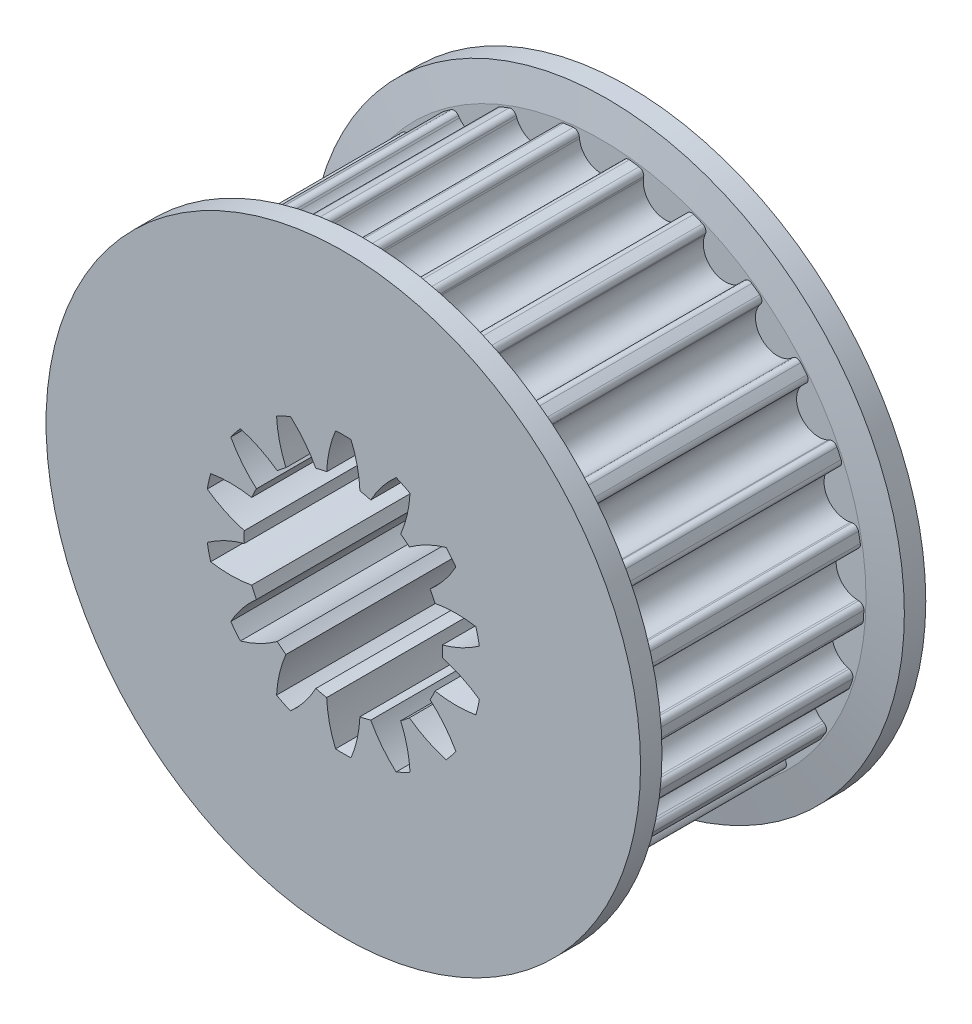
SolidWorks part; units mm, degrees
material "PETG"
ref_plane "Front Plane" through (0, 0, 0) normal (0, 0, 1) x (1, 0, 0)
ref_plane "Top Plane" through (0, 0, 0) normal (0, 1, 0) x (1, 0, 0)
ref_plane "Right Plane" through (0, 0, 0) normal (1, 0, 0) x (0, 0, -1)
sketch "Sketch2" plane through (0, 0, 0) normal (0, 0, 1) x (1, 0, 0)
  circle A0 centre (0, 0) radius 19.3468
  dimension "D1" = 38.6936
extrude "pulley" add sketch "Sketch2" along normal mid plane 17
sketch "tooth" plane through (0, 0, 0) normal (0, 0, 1) x (1, 0, 0)
  line L0 (0, 0) -> (0, 18.9468) construction
  line L1 (4.9563, 18.2871) -> (0, 18.9468) construction
  line L2 (4.9563, 18.2871) -> (0, 0) construction
  line L3 (-2.1327, 22.9824) -> (-1.6129, 18.7488)
  line L6 (2.1327, 22.9824) -> (1.6129, 18.7488)
  line L7 (-2.1327, 22.9824) -> (2.1327, 22.9824)
  arc A1 (-1.6129, 18.7488) -> (1.6129, 18.7488) centre (0, 18.9468) ccw
  arc A2 (0, 18.9468) -> (4.9563, 18.2871) centre (0, 0) cw construction
  circle A3 centre (4.9563, 18.2871) radius 1.625 construction
  dimension "D1" = 18.9468
  dimension "D2" = 3.25
  dimension "D3" = 5
  dimension "D5" = 14
extrude "cut tooth" cut sketch "tooth" against normal mid plane 17
fillet "blend tooth" radius 0.4 2 edges at (1.6774, 19.274, 0) (-1.6774, 19.274, 0)
pattern_circular "tooth pattern" count 25 over 360 about axis through (0, 0, 0) along (0, 0, 1) of "cut tooth", "blend tooth"
sketch "Sketch3" plane through (0, 0, 0) normal (0, 0, 1) x (1, 0, 0)
  circle A0 centre (0, 0) radius 21.8868
  circle A1 centre (0, 0) radius 19.3468 construction
  dimension "D1" = 2.54
extrude "sidewall" add sketch "Sketch3" along normal blind 2 from offset 8.5
mirror "mirror sidewall" about plane through (0, 0, 0) normal (0, 0, 1) of "sidewall"
chamfer "sidewall chamfer" distance 2.4 angle 10 2 edges at (21.8868, 0, 8.5) (21.8868, 0, -8.5)
sketch "Sketch5" plane through (0, 0, 0) normal (0, 0, 1) x (1, 0, 0)
  circle A0 centre (0, 0) radius 9.525
  dimension "D1" = 19.05
extrude "bearing spacer (Manual Suppress)" add sketch "Sketch5" along normal blind 10.55 and the other way blind 10.55
sketch "Sketch6" plane through (0, 0, -10.5) normal (0, 0, -1) x (-1, 0, 0)
  arc A57 (2.0216, -7.0171) -> (3.8881, -9.3866) centre (9.6274, -2.9458) ccw
  arc A58 (1.2232, -7.1993) -> (2.0216, -7.0171) centre (0, 0) ccw
  arc A59 (0.5697, -10.144) -> (1.2232, -7.1993) centre (-7.3959, -6.8313) ccw
  arc A60 (-0.5697, -10.144) -> (0.5697, -10.144) centre (0, 0) ccw
  arc A61 (-1.2232, -7.1993) -> (-0.5697, -10.144) centre (7.3959, -6.8313) ccw
  arc A62 (-2.0216, -7.0171) -> (-1.2232, -7.1993) centre (0, 0) ccw
  arc A63 (-3.8881, -9.3866) -> (-2.0216, -7.0171) centre (-9.6274, -2.9458) ccw
  arc A64 (-4.9146, -8.8923) -> (-3.8881, -9.3866) centre (0, 0) ccw
  arc A65 (-4.2257, -5.9556) -> (-4.9146, -8.8923) centre (3.6995, -9.3637) ccw
  arc A66 (-4.866, -5.4451) -> (-4.2257, -5.9556) centre (0, 0) ccw
  arc A67 (-7.5757, -6.7701) -> (-4.866, -5.4451) centre (-9.9522, 1.5231) ccw
  arc A68 (-8.2861, -5.8793) -> (-7.5757, -6.7701) centre (0, 0) ccw
  arc A69 (-6.3913, -3.5324) -> (-8.2861, -5.8793) centre (-0.7297, -10.0416) ccw
  arc A70 (-6.7466, -2.7945) -> (-6.3913, -3.5324) centre (0, 0) ccw
  arc A71 (-9.7629, -2.8126) -> (-6.7466, -2.7945) centre (-8.3058, 5.6903) ccw
  arc A72 (-10.0164, -1.7019) -> (-9.7629, -2.8126) centre (0, 0) ccw
  arc A73 (-7.291, -0.4095) -> (-10.0164, -1.7019) centre (-5.0143, -8.7306) ccw
  arc A74 (-7.291, 0.4095) -> (-7.291, -0.4095) centre (0, 0) ccw
  arc A75 (-10.0164, 1.7019) -> (-7.291, 0.4095) centre (-5.0143, 8.7306) ccw
  arc A76 (-9.7629, 2.8126) -> (-10.0164, 1.7019) centre (0, 0) ccw
  arc A77 (-6.7466, 2.7945) -> (-9.7629, 2.8126) centre (-8.3058, -5.6903) ccw
  arc A78 (-6.3913, 3.5324) -> (-6.7466, 2.7945) centre (0, 0) ccw
  arc A79 (-8.2861, 5.8793) -> (-6.3913, 3.5324) centre (-0.7297, 10.0416) ccw
  arc A80 (-7.5757, 6.7701) -> (-8.2861, 5.8793) centre (0, 0) ccw
  arc A81 (-4.866, 5.4451) -> (-7.5757, 6.7701) centre (-9.9522, -1.5231) ccw
  arc A82 (-4.2257, 5.9556) -> (-4.866, 5.4451) centre (0, 0) ccw
  arc A83 (-4.9146, 8.8923) -> (-4.2257, 5.9556) centre (3.6995, 9.3637) ccw
  arc A84 (-3.8881, 9.3866) -> (-4.9146, 8.8923) centre (0, 0) ccw
  arc A85 (-2.0216, 7.0171) -> (-3.8881, 9.3866) centre (-9.6274, 2.9458) ccw
  arc A86 (-1.2232, 7.1993) -> (-2.0216, 7.0171) centre (0, 0) ccw
  arc A87 (-0.5697, 10.144) -> (-1.2232, 7.1993) centre (7.3959, 6.8313) ccw
  arc A88 (0.5697, 10.144) -> (-0.5697, 10.144) centre (0, 0) ccw
  arc A89 (1.2232, 7.1993) -> (0.5697, 10.144) centre (-7.3959, 6.8313) ccw
  arc A90 (2.0216, 7.0171) -> (1.2232, 7.1993) centre (0, 0) ccw
  arc A91 (3.8881, 9.3866) -> (2.0216, 7.0171) centre (9.6274, 2.9458) ccw
  arc A92 (4.9146, 8.8923) -> (3.8881, 9.3866) centre (0, 0) ccw
  arc A93 (4.2257, 5.9556) -> (4.9146, 8.8923) centre (-3.6995, 9.3637) ccw
  arc A94 (4.866, 5.4451) -> (4.2257, 5.9556) centre (0, 0) ccw
  arc A95 (7.5757, 6.7701) -> (4.866, 5.4451) centre (9.9522, -1.5231) ccw
  arc A96 (8.2861, 5.8793) -> (7.5757, 6.7701) centre (0, 0) ccw
  arc A97 (6.3913, 3.5324) -> (8.2861, 5.8793) centre (0.7297, 10.0416) ccw
  arc A98 (6.7466, 2.7945) -> (6.3913, 3.5324) centre (0, 0) ccw
  arc A99 (9.7629, 2.8126) -> (6.7466, 2.7945) centre (8.3058, -5.6903) ccw
  arc A100 (10.0164, 1.7019) -> (9.7629, 2.8126) centre (0, 0) ccw
  arc A101 (7.291, 0.4095) -> (10.0164, 1.7019) centre (5.0143, 8.7306) ccw
  arc A102 (7.291, -0.4095) -> (7.291, 0.4095) centre (0, 0) ccw
  arc A103 (10.0164, -1.7019) -> (7.291, -0.4095) centre (5.0143, -8.7306) ccw
  arc A104 (9.7629, -2.8126) -> (10.0164, -1.7019) centre (0, 0) ccw
  arc A105 (6.7466, -2.7945) -> (9.7629, -2.8126) centre (8.3058, 5.6903) ccw
  arc A106 (6.3913, -3.5324) -> (6.7466, -2.7945) centre (0, 0) ccw
  arc A107 (8.2861, -5.8793) -> (6.3913, -3.5324) centre (0.7297, -10.0416) ccw
  arc A108 (7.5757, -6.7701) -> (8.2861, -5.8793) centre (0, 0) ccw
  arc A109 (4.866, -5.4451) -> (7.5757, -6.7701) centre (9.9522, 1.5231) ccw
  arc A110 (4.2257, -5.9556) -> (4.866, -5.4451) centre (0, 0) ccw
  arc A111 (4.9146, -8.8923) -> (4.2257, -5.9556) centre (-3.6995, -9.3637) ccw
  arc A112 (3.8881, -9.3866) -> (4.9146, -8.8923) centre (0, 0) ccw
  arc A113 (2.0216, -7.0171) -> (3.8881, -9.3866) centre (9.6274, -2.9458) ccw
  arc A114 (1.2232, -7.1993) -> (2.0216, -7.0171) centre (0, 0) ccw
  arc A115 (0.5697, -10.144) -> (1.2232, -7.1993) centre (-7.3959, -6.8313) ccw
  arc A116 (-0.5697, -10.144) -> (0.5697, -10.144) centre (0, 0) ccw
  arc A117 (-1.2232, -7.1993) -> (-0.5697, -10.144) centre (7.3959, -6.8313) ccw
  arc A118 (-2.0216, -7.0171) -> (-1.2232, -7.1993) centre (0, 0) ccw
  arc A119 (-3.8881, -9.3866) -> (-2.0216, -7.0171) centre (-9.6274, -2.9458) ccw
  arc A120 (-4.9146, -8.8923) -> (-3.8881, -9.3866) centre (0, 0) ccw
  arc A121 (-4.2257, -5.9556) -> (-4.9146, -8.8923) centre (3.6995, -9.3637) ccw
  arc A122 (-4.866, -5.4451) -> (-4.2257, -5.9556) centre (0, 0) ccw
  arc A123 (-7.5757, -6.7701) -> (-4.866, -5.4451) centre (-9.9522, 1.5231) ccw
  arc A124 (-8.2861, -5.8793) -> (-7.5757, -6.7701) centre (0, 0) ccw
  arc A125 (-6.3913, -3.5324) -> (-8.2861, -5.8793) centre (-0.7297, -10.0416) ccw
  arc A126 (-6.7466, -2.7945) -> (-6.3913, -3.5324) centre (0, 0) ccw
  arc A127 (-9.7629, -2.8126) -> (-6.7466, -2.7945) centre (-8.3058, 5.6903) ccw
  arc A128 (-10.0164, -1.7019) -> (-9.7629, -2.8126) centre (0, 0) ccw
  arc A129 (-7.291, -0.4095) -> (-10.0164, -1.7019) centre (-5.0143, -8.7306) ccw
  arc A130 (-7.291, 0.4095) -> (-7.291, -0.4095) centre (0, 0) ccw
  arc A131 (-10.0164, 1.7019) -> (-7.291, 0.4095) centre (-5.0143, 8.7306) ccw
  arc A132 (-9.7629, 2.8126) -> (-10.0164, 1.7019) centre (0, 0) ccw
  arc A133 (-6.7466, 2.7945) -> (-9.7629, 2.8126) centre (-8.3058, -5.6903) ccw
  arc A134 (-6.3913, 3.5324) -> (-6.7466, 2.7945) centre (0, 0) ccw
  arc A135 (-8.2861, 5.8793) -> (-6.3913, 3.5324) centre (-0.7297, 10.0416) ccw
  arc A136 (-7.5757, 6.7701) -> (-8.2861, 5.8793) centre (0, 0) ccw
  arc A137 (-4.866, 5.4451) -> (-7.5757, 6.7701) centre (-9.9522, -1.5231) ccw
  arc A138 (-4.2257, 5.9556) -> (-4.866, 5.4451) centre (0, 0) ccw
  arc A139 (-4.9146, 8.8923) -> (-4.2257, 5.9556) centre (3.6995, 9.3637) ccw
  arc A140 (-3.8881, 9.3866) -> (-4.9146, 8.8923) centre (0, 0) ccw
  arc A141 (-2.0216, 7.0171) -> (-3.8881, 9.3866) centre (-9.6274, 2.9458) ccw
  arc A142 (-1.2232, 7.1993) -> (-2.0216, 7.0171) centre (0, 0) ccw
  arc A143 (-0.5697, 10.144) -> (-1.2232, 7.1993) centre (7.3959, 6.8313) ccw
  arc A144 (0.5697, 10.144) -> (-0.5697, 10.144) centre (0, 0) ccw
  arc A145 (1.2232, 7.1993) -> (0.5697, 10.144) centre (-7.3959, 6.8313) ccw
  arc A146 (2.0216, 7.0171) -> (1.2232, 7.1993) centre (0, 0) ccw
  arc A147 (3.8881, 9.3866) -> (2.0216, 7.0171) centre (9.6274, 2.9458) ccw
  arc A148 (4.9146, 8.8923) -> (3.8881, 9.3866) centre (0, 0) ccw
  arc A149 (4.2257, 5.9556) -> (4.9146, 8.8923) centre (-3.6995, 9.3637) ccw
  arc A150 (4.866, 5.4451) -> (4.2257, 5.9556) centre (0, 0) ccw
  arc A151 (7.5757, 6.7701) -> (4.866, 5.4451) centre (9.9522, -1.5231) ccw
  arc A152 (8.2861, 5.8793) -> (7.5757, 6.7701) centre (0, 0) ccw
  arc A153 (6.3913, 3.5324) -> (8.2861, 5.8793) centre (0.7297, 10.0416) ccw
  arc A154 (6.7466, 2.7945) -> (6.3913, 3.5324) centre (0, 0) ccw
  arc A155 (9.7629, 2.8126) -> (6.7466, 2.7945) centre (8.3058, -5.6903) ccw
  arc A156 (10.0164, 1.7019) -> (9.7629, 2.8126) centre (0, 0) ccw
  arc A157 (7.291, 0.4095) -> (10.0164, 1.7019) centre (5.0143, 8.7306) ccw
  arc A158 (7.291, -0.4095) -> (7.291, 0.4095) centre (0, 0) ccw
  arc A159 (10.0164, -1.7019) -> (7.291, -0.4095) centre (5.0143, -8.7306) ccw
  arc A160 (9.7629, -2.8126) -> (10.0164, -1.7019) centre (0, 0) ccw
  arc A161 (6.7466, -2.7945) -> (9.7629, -2.8126) centre (8.3058, 5.6903) ccw
  arc A162 (6.3913, -3.5324) -> (6.7466, -2.7945) centre (0, 0) ccw
  arc A163 (8.2861, -5.8793) -> (6.3913, -3.5324) centre (0.7297, -10.0416) ccw
  arc A164 (7.5757, -6.7701) -> (8.2861, -5.8793) centre (0, 0) ccw
  arc A165 (4.866, -5.4451) -> (7.5757, -6.7701) centre (9.9522, 1.5231) ccw
  arc A166 (4.2257, -5.9556) -> (4.866, -5.4451) centre (0, 0) ccw
  arc A167 (4.9146, -8.8923) -> (4.2257, -5.9556) centre (-3.6995, -9.3637) ccw
  arc A168 (3.8881, -9.3866) -> (4.9146, -8.8923) centre (0, 0) ccw
  dimension "D1" = 0
extrude "Cut-Extrude1" cut sketch "Sketch6" against normal through all and the other way through all
sketch "Sketch7" plane through (0, 0, 0) normal (0, 1, 0) x (1, 0, 0)
  line L0 (-0.5697, 10.5) -> (-0.811, 10.5) construction
  line L1 (-13.7518, -10.5) -> (14.8154, -10.5)
  line L2 (-13.7518, -10.5) -> (-13.7518, -34.3505)
  line L3 (-13.7518, -34.3505) -> (14.8154, -34.3505)
  line L4 (14.8154, -10.5) -> (14.8154, -34.3505)
  line L5 (-15.7032, 10.5) -> (16.0301, 10.5)
  line L6 (-15.7032, 10.5) -> (-15.7032, 32.5123)
  line L7 (-15.7032, 32.5123) -> (16.0301, 32.5123)
  line L8 (16.0301, 10.5) -> (16.0301, 32.5123)
  line L9 (-0.811, -10.5) -> (-0.5697, -10.5) construction
extrude "Cut-Extrude2" cut sketch "Sketch7" against normal through all and the other way through all
equation "\"INPUT_pulley_teeth\"= 25"
equation "\"pulley_c2c\"= 5mm"
equation "\"pulley_teeth_deg\" = 360deg / \"INPUT_pulley_teeth\""
equation "\"pulley_radius\"= ( \"pulley_c2c\" / ( 2 * cos ( \"iso_half_angle\" ) ) ) - 1mm"
equation "\"iso_half_angle\" = ( 180deg - \"pulley_teeth_deg\" ) / 2"
equation "\"D1@tooth\" = \"pulley_radius\""
equation "\"pulley_tooth_dia\"= 3.25mm"
equation "\"D3@tooth\"=\"pulley_c2c\""
equation "\"D2@tooth\"=\"pulley_tooth_dia\""
equation "\"D1@Sketch2\"=2* \"pulley_radius\"+\"pulley_tooth_offset\""
equation "\"pulley_tooth_offset\"= .8mm"
equation "\"D1@tooth pattern\" = \"INPUT_pulley_teeth\""
equation "\"INPUT_pulley_belt_9_or_15_(unitless)\"= 15"
equation "\"D1@pulley\"=\"pulley_width\""
equation "\"D19@sidewall\" =  ( \"pulley_width\" / 2 ) "
equation "\"D1@sidewall\"=\"pulley_sidewall_thick\""
equation "\"pulley_width\"= 17mm"
equation "\"D1@cut tooth\"=\"pulley_width\""
equation "\"D1@sidewall chamfer\" = 2.4mm"
equation "\"D1@bearing spacer (Manual Suppress)\" = 0.05mm + ( \"pulley_width\" / 2 ) + \"pulley_sidewall_thick\""
equation "\"D2@bearing spacer (Manual Suppress)\" = 0.05mm + ( \"pulley_width\" / 2 ) + \"pulley_sidewall_thick\""
equation "\"pulley_sidewall_thick\"= 2mm"
equation "\"D1\"= \"pulley_width\""
equation "\"D19\" = ( \"pulley_width\" / 2 ) + \"pulley_sidewall_thick\" - 0.02mm"
